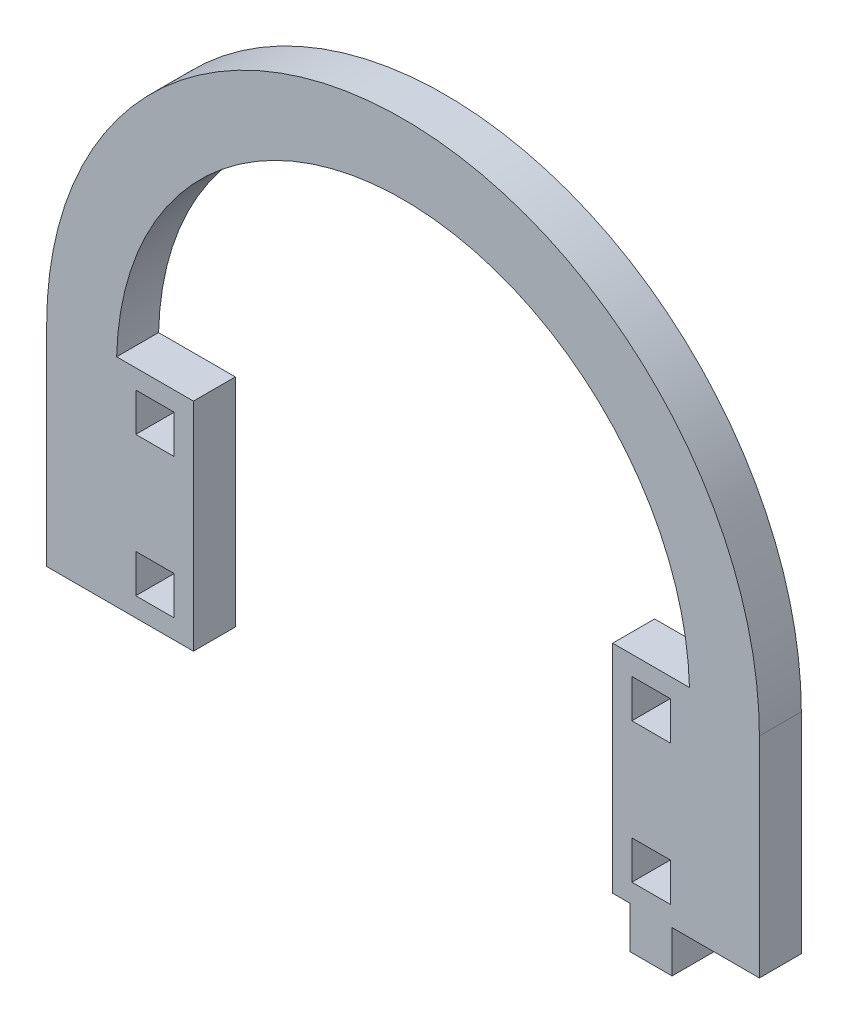
SolidWorks part; units mm, degrees
ref_plane "Front Plane" through (0, 0, 0) normal (0, 0, 1) x (1, 0, 0)
ref_plane "Top Plane" through (0, 0, 0) normal (0, 1, 0) x (1, 0, 0)
ref_plane "Right Plane" through (0, 0, 0) normal (1, 0, 0) x (0, 0, -1)
sketch "Model" plane through (0, 0, 0) normal (0, 0, 1) x (1, 0, 0)
  line L0 (3257.6135, 1322.3552) -> (3257.6135, 1292.3552)
  line L1 (3359.6135, 1322.3552) -> (3359.6135, 1292.3552)
  line L2 (3257.6135, 1292.3552) -> (3267.6135, 1292.3552)
  line L3 (3346.8635, 1300.6052) -> (3341.3635, 1300.6052)
  line L4 (3341.3635, 1300.6052) -> (3341.3635, 1295.1052)
  line L5 (3341.3635, 1295.1052) -> (3346.8635, 1295.1052)
  line L6 (3346.8635, 1295.1052) -> (3346.8635, 1300.6052)
  line L7 (3338.6135, 1292.3552) -> (3341.1135, 1292.3552)
  line L8 (3341.1135, 1292.3552) -> (3341.1135, 1286.3552)
  line L9 (3341.1135, 1286.3552) -> (3347.1135, 1286.3552)
  line L10 (3347.1135, 1286.3552) -> (3347.1135, 1292.3552)
  line L11 (3346.8635, 1320.6052) -> (3341.3635, 1320.6052)
  line L12 (3341.3635, 1320.6052) -> (3341.3635, 1315.1052)
  line L13 (3341.3635, 1315.1052) -> (3346.8635, 1315.1052)
  line L14 (3346.8635, 1315.1052) -> (3346.8635, 1320.6052)
  line L15 (3275.8635, 1300.6052) -> (3270.3635, 1300.6052)
  line L16 (3270.3635, 1300.6052) -> (3270.3635, 1295.1052)
  line L17 (3270.3635, 1295.1052) -> (3275.8635, 1295.1052)
  line L18 (3275.8635, 1295.1052) -> (3275.8635, 1300.6052)
  line L19 (3267.6135, 1292.3552) -> (3278.6135, 1292.3552)
  line L20 (3275.8635, 1320.6052) -> (3270.3635, 1320.6052)
  line L21 (3270.3635, 1320.6052) -> (3270.3635, 1315.1052)
  line L22 (3270.3635, 1315.1052) -> (3275.8635, 1315.1052)
  line L23 (3275.8635, 1315.1052) -> (3275.8635, 1320.6052)
  line L24 (3278.6135, 1323.3552) -> (3278.6135, 1292.3552)
  line L25 (3338.6135, 1323.3552) -> (3338.6135, 1292.3552)
  line L26 (3347.1135, 1292.3552) -> (3359.6135, 1292.3552)
  line L27 (3267.6256, 1323.3552) -> (3278.6135, 1323.3552)
  line L28 (3338.6135, 1323.3552) -> (3349.6013, 1323.3552)
  arc A0 (3359.6135, 1322.3552) -> (3257.6135, 1322.3552) centre (3308.6135, 1322.3552) ccw
  arc A1 (3349.6013, 1323.3552) -> (3267.6256, 1323.3552) centre (3308.6135, 1322.3552) ccw
extrude "Boss-Extrude1" add sketch "Model" along normal blind 6 contours L22 L23 L20 L21 | L17 L18 L15 L16 | L13 L14 L11 L12 | L5 L6 L3 L4 | L1 L26 L10 L9 L8 L7 L25 L28 A1 L27 L24 L19 L2 L0 A0
